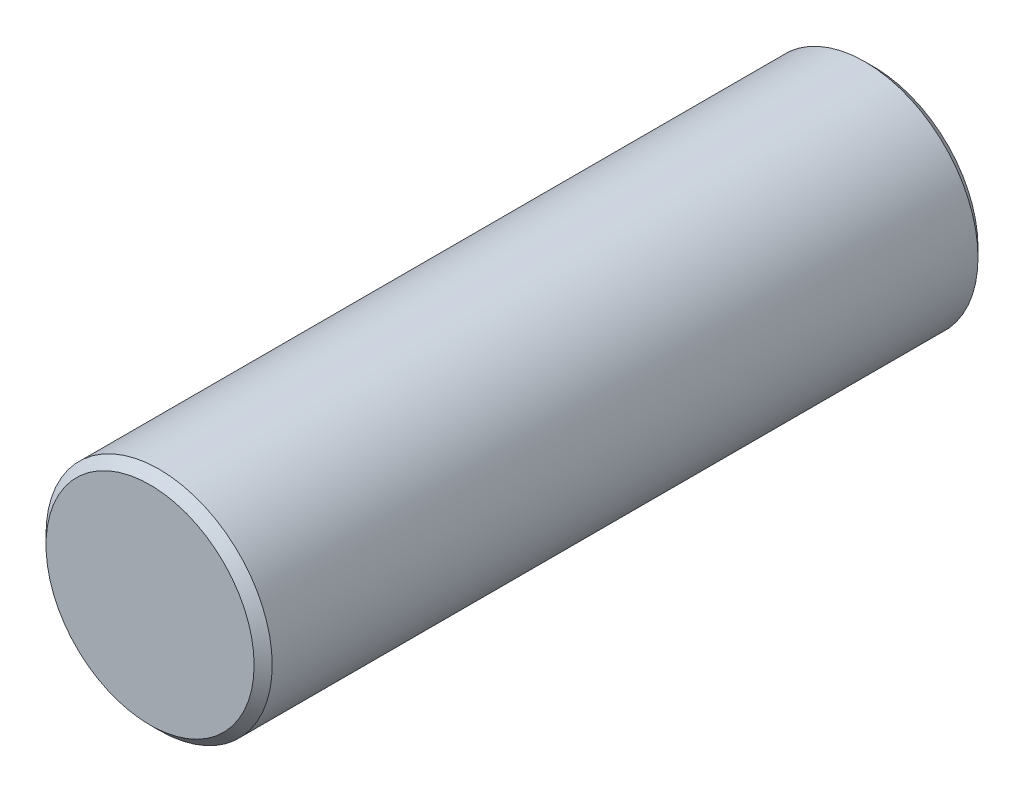
SolidWorks part; units mm, degrees
ref_plane "Front Plane" through (0, 0, 0) normal (0, 0, 1) x (1, 0, 0)
ref_plane "Top Plane" through (0, 0, 0) normal (0, 1, 0) x (1, 0, 0)
ref_plane "Right Plane" through (0, 0, 0) normal (1, 0, 0) x (0, 0, -1)
sketch "Sketch1" plane through (0, 0, 0) normal (0, 0, 1) x (1, 0, 0)
  circle A0 centre (0, 0) radius 2.5
  dimension "D1" = 5
extrude "Boss-Extrude1" add sketch "Sketch1" along normal blind 16
chamfer "Chamfer1" distance 0.2 angle 45 2 edges at (2.5, 0, 0) (2.5, 0, 16)
